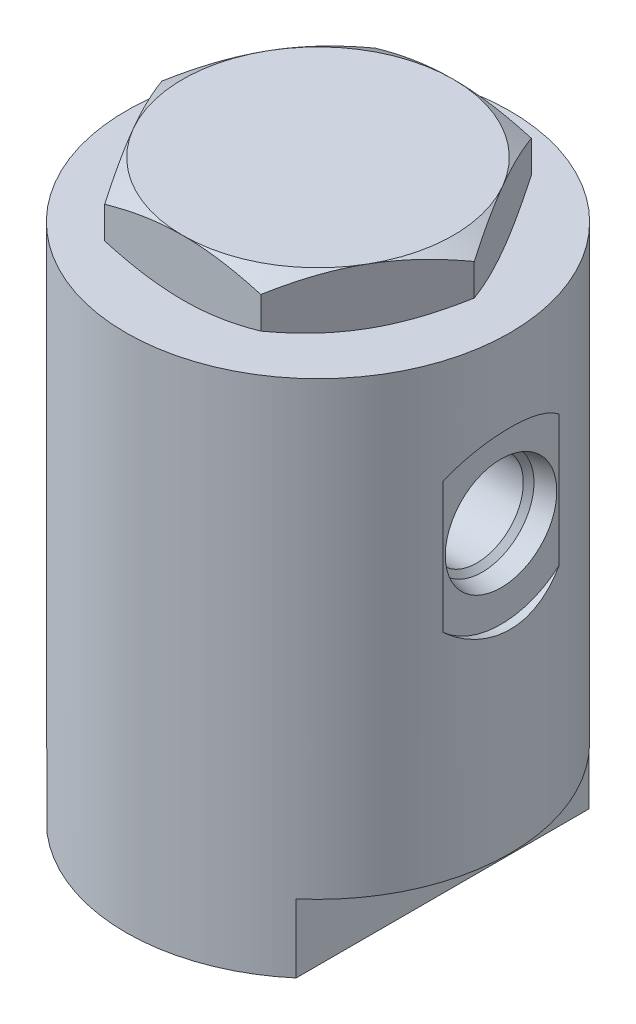
SolidWorks part; units mm, degrees
material "Alloy Steel"
ref_plane "Front Plane" through (0, 0, 0) normal (0, 0, 1) x (1, 0, 0)
ref_plane "Top Plane" through (0, 0, 0) normal (0, 1, 0) x (1, 0, 0)
ref_plane "Right Plane" through (0, 0, 0) normal (1, 0, 0) x (0, 0, -1)
ref_plane "Plane1" through (0, 0, 0) normal (0, 1, 0) x (1, 0, 0)
sketch "Sketch1" plane through (0, 0, 0) normal (0, 1, 0) x (1, 0, 0)
  circle A0 centre (0, 0) radius 27.051
  dimension "D1" = 54.102
extrude "Extrude1" add sketch "Sketch1" along normal blind 73.152
sketch "Sketch2" plane through (0, 0, 0) normal (0, -1, 0) x (1, 0, 0)
  line L0 (17.526, 20.6057) -> (17.526, -20.6057)
  line L2 (-17.526, -20.6057) -> (-17.526, 20.6057)
  line L4 (0, -29.7561) -> (0, 29.7561) construction
  arc A0 (-17.526, 20.6057) -> (-17.526, -20.6057) centre (0, 0) ccw
  circle A1 centre (0, 0) radius 27.051
  arc A2 (17.526, -20.6057) -> (17.526, 20.6057) centre (0, 0) ccw
  dimension "D2" = 35.052
  dimension "D1" = 0
extrude "Cut-Extrude1" cut sketch "Sketch2" against normal blind 9.652
ref_plane "Plane2" through (27.051, 49.276, 0) normal (0, 0, 1) x (0, -1, 0)
sketch "S2D0007" plane through (27.051, 49.276, 0) normal (0, 0, 1) x (0, -1, 0)
  line L0 (0, 0) -> (12.319, 0)
  line L1 (12.319, 0) -> (12.319, -1.27)
  line L2 (12.319, -1.27) -> (7.855, -1.27)
  line L3 (7.855, -1.27) -> (7.2908, -3.9243)
  line L4 (7.2908, -3.9243) -> (6.5405, -4.6746)
  line L5 (6.5405, -4.6746) -> (6.5405, -16.7386)
  line L6 (6.5405, -16.7386) -> (0, -20.6685)
  line L7 (0, -20.6685) -> (0, 0)
  line L8 (0, -31.4992) -> (0, 1.0334) construction
  line L9 (39.624, 0) -> (-23.876, 0) construction
  line L10 (49.276, -44.577) -> (49.276, -9.525) construction
  dimension "D1" = 1.27
  dimension "D2" = 49.276
  dimension "D3" = 24.638
  dimension "D4" = 12
  dimension "D5" = 15.7099
  dimension "D6" = 45
  dimension "D7" = 2.6543
  dimension "D8" = 13.081
  dimension "D9" = 59
  dimension "D10" = 15.4686
revolve "Cut-Revolve1" cut sketch "S2D0007" angle 360 about L8
ref_plane "Plane3" through (0, 0, 0) normal (0, 0, 1) x (-1, 0, 0)
sketch "Sketch4" plane through (0, 0, 0) normal (0, 0, 1) x (-1, 0, 0)
  line L0 (0, 0) -> (12.319, 0)
  line L1 (12.319, 0) -> (12.319, -0.254)
  line L2 (12.319, -0.254) -> (7.855, -0.254)
  line L3 (7.855, -0.254) -> (7.2908, -2.9083)
  line L4 (7.2908, -2.9083) -> (6.5405, -3.6586)
  line L5 (6.5405, -3.6586) -> (6.5405, -15.7226)
  line L6 (6.5405, -15.7226) -> (0, -19.6525)
  line L7 (0, -19.6525) -> (0, 0)
  line L8 (0, -25.8993) -> (0, 0.9826) construction
  line L9 (17.526, 0) -> (-17.526, 0) construction
  point P10 (0, 0)
  dimension "D1" = 0.254
  dimension "D2" = 13.081
  dimension "D3" = 24.638
  dimension "D4" = 15.7226
  dimension "D5" = 59
  dimension "D6" = 45
  dimension "D7" = 2.6543
  dimension "D8" = 12
  dimension "D9" = 15.7099
revolve "Cut-Revolve2" cut sketch "Sketch4" angle 360 about L8
sketch "Sketch5" plane through (0, 73.152, 0) normal (0, 1, 0) x (-1, 0, 0)
  line L1 (21.997, 0) -> (10.9985, 19.05)
  line L2 (10.9985, 19.05) -> (-10.9985, 19.05)
  line L3 (-10.9985, 19.05) -> (-21.997, 0)
  line L4 (-21.997, 0) -> (-10.9985, -19.05)
  line L5 (-10.9985, -19.05) -> (10.9985, -19.05)
  line L6 (10.9985, -19.05) -> (21.997, 0)
  circle A0 centre (0, 0) radius 19.05 construction
  dimension "D1" = 38.1
extrude "Extrude2" add sketch "Sketch5" along normal blind 7.874
ref_plane "Plane4" through (0, 0, 0) normal (1, 0, 0) x (0, 0, -1)
sketch "Sketch6" plane through (0, 0, 0) normal (1, 0, 0) x (0, 0, -1)
  line L0 (19.05, 81.026) -> (25.8691, 77.089)
  line L1 (19.05, 73.152) -> (25.8691, 77.089)
  line L2 (19.05, 81.026) -> (31.75, 81.026)
  line L3 (31.75, 81.026) -> (31.75, 73.152)
  line L4 (31.75, 73.152) -> (19.05, 73.152)
  line L5 (0, 72.7583) -> (0, 81.4197) construction
  line L6 (19.05, 81.026) -> (19.05, 73.152) construction
  line L7 (0, 81.026) -> (19.05, 81.026) construction
  line L8 (0, 73.152) -> (19.05, 73.152) construction
  line L9 (31.75, 77.089) -> (25.8691, 77.089) construction
  dimension "D1" = 60
  dimension "D2" = 63.5
revolve "Cut-Revolve3" cut sketch "Sketch6" angle 360 about L5
sketch "Sketch7" plane through (0, 0, 0) normal (0, 0, 1) x (1, 0, 0)
  line L0 (0, 0) -> (0, 89.3367) construction
  line L1 (27.051, 73.152) -> (-27.051, 73.152) construction
  line L2 (-15.875, 73.152) -> (0, 73.152)
  line L3 (-15.875, 73.152) -> (-15.875, 12.827)
  line L4 (-15.875, 12.827) -> (0, 12.827)
  line L5 (0, 73.152) -> (0, 12.827)
  line L6 (-17.526, 0) -> (17.526, 0) construction
  dimension "D1" = 31.75
  dimension "D2" = 12.827
revolve "Cut-Revolve4" cut sketch "Sketch7" angle 360 about L0
